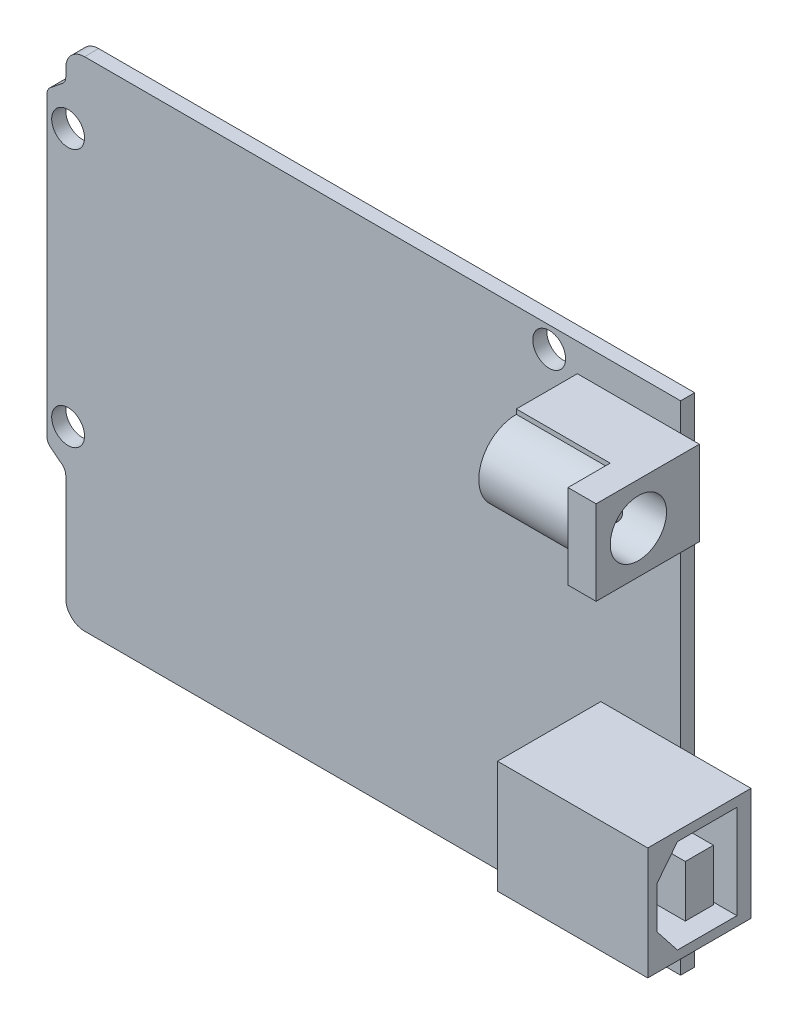
SolidWorks part; units mm, degrees
ref_plane "Front Plane" through (0, 0, 0) normal (0, 0, 1) x (1, 0, 0)
ref_plane "Top Plane" through (0, 0, 0) normal (0, 1, 0) x (1, 0, 0)
ref_plane "Right Plane" through (0, 0, 0) normal (1, 0, 0) x (0, 0, -1)
sketch "Sketch1" plane through (0, 0, 0) normal (0, 0, 1) x (1, 0, 0)
  line L0 (30, 26.5) -> (30, -26.5)
  line L1 (-37.5, 26.5) -> (37.5, 26.5)
  line L2 (-37.5, 26.5) -> (-37.5, -26.5)
  line L3 (-37.5, -26.5) -> (37.5, -26.5)
  line L4 (37.5, 26.5) -> (37.5, -26.5)
  line L5 (-37.5, 26.5) -> (37.5, -26.5) construction
  line L6 (-37.5, -26.5) -> (37.5, 26.5) construction
  circle A0 centre (-35.25, 19) radius 1.75
  circle A1 centre (-35.25, -8.5) radius 1.75
  circle A2 centre (16, 24.25) radius 1.75
  circle A3 centre (16, -24.25) radius 1.75
  point P0 (0, 0)
  dimension "D4" = 3.5
  dimension "D1" = 75
  dimension "D2" = 53
  dimension "D3" = 7.5
  dimension "D5" = 14
  dimension "D6" = 2.25
  dimension "D7" = 2.25
  dimension "D8" = 2.25
  dimension "D9" = 7.5
  dimension "D10" = 27.5
extrude "Boss-Extrude1" add sketch "Sketch1" along normal blind 1.5 contours L2 L3 L0 L1 A3 A2 A1 A0 | L4 L1 L0 L3
sketch "Sketch2" plane through (0, 0, 1.5) normal (0, 0, 1) x (1, 0, 0)
  line L0 (-37.5, -26.5) -> (37.5, -26.5) construction
  line L1 (-37.5, 26.5) -> (37.5, 26.5) construction
  line L2 (-37.5, 26.5) -> (-37.5, -26.5) construction
  line L3 (37.5, 26.5) -> (37.5, -26.5) construction
  line L4 (30, 26.5) -> (30, -26.5) construction
  line L5 (-37.5, -26.5) -> (37.5, -26.5)
  line L6 (-37.5, 26.5) -> (37.5, 26.5)
  line L7 (-37.5, 26.5) -> (-37.5, -26.5)
  line L8 (37.5, 26.5) -> (37.5, -26.5)
  line L9 (30, 26.5) -> (30, -26.5)
  line L10 (-37.5, 21.5442) -> (-35.5, 23.1319)
  line L11 (-35.5, 23.1319) -> (-35.5, 26.5)
  line L12 (-35.25, 19) -> (-35.25, -8.5) construction
  line L13 (-35.25, 5.25) -> (-14.1194, 5.25) construction
  line L14 (-35.5, -12.6319) -> (-35.5, -16)
  line L15 (-37.5, -11.0442) -> (-35.5, -12.6319)
  line L16 (-35.5, -16) -> (-35.5, -26.5)
  line M8 (-37.5, 26.5) -> (-37.5, -26.5)
  line M9 (-37.5, -26.5) -> (37.5, -26.5)
  line M11 (37.5, 26.5) -> (-37.5, 26.5)
  dimension "D1" = 2
extrude "Cut-Extrude1" cut sketch "Sketch2" against normal blind 2 contours L10 L11 M11 M8 | L16 L14 L15 M8 M9
fillet "Fillet1" radius 1 4 edges at (-35.5, 23.1319, 0.75) (-37.5, 21.5442, 0.75) (-35.5, -12.6319, 0.75) (-37.5, -11.0442, 0.75)
fillet "Fillet2" radius 2 2 edges at (-35.5, -26.5, 0.75) (-35.5, 26.5, 0.75)
sketch "Sketch3" plane through (0, 0, 1.5) normal (0, 0, 1) x (1, 0, 0)
  line L0 (-37.5, -26.5) -> (37.5, -26.5) construction
  line L1 (-37.5, 26.5) -> (37.5, 26.5) construction
  line L2 (37.5, 26.5) -> (37.5, -26.5) construction
  line L3 (-37.5, -26.5) -> (37.5, -26.5)
  line L4 (-37.5, 26.5) -> (37.5, 26.5)
  line L5 (37.5, 26.5) -> (37.5, -26.5)
  line L6 (30, 26.5) -> (30, 23.5)
  line L7 (30, 23.5) -> (32, 23.5)
  line L8 (32, 23.5) -> (32, 14.5)
  line L9 (32, 14.5) -> (30, 14.5)
  line L10 (30, 14.5) -> (30, -5.5)
  line L11 (30, -5.5) -> (37.5, -5.5)
  line L12 (37.5, -5.5) -> (37.5, -17.5)
  line L13 (37.5, -17.5) -> (30, -17.5)
  line L14 (30, -17.5) -> (30, -26.5)
  line L15 (30, 26.5) -> (30, -26.5) construction
  line M10 (37.5, -26.5) -> (37.5, 26.5)
  line M11 (37.5, 26.5) -> (-33.5, 26.5)
  dimension "D1" = 2
  dimension "D2" = 3
  dimension "D3" = 9
  dimension "D4" = 7.5
  dimension "D5" = 9
  dimension "D6" = 12
extrude "Cut-Extrude2" cut sketch "Sketch3" against normal blind 2 contours L10 L11 L5 L6 L7 L8 L9 M11 | L13 L14 L3 M10
sketch "Sketch4" plane through (0, 0, 1.5) normal (0, 0, 1) x (1, 0, 0)
  line L0 (37.5, -17.5) -> (30, -17.5) construction
  line L1 (37.5, -5.5) -> (37.5, -17.5) construction
  line L2 (30, -5.5) -> (37.5, -5.5) construction
  line L3 (37.5, -17.5) -> (30, -17.5)
  line L4 (37.5, -5.5) -> (37.5, -17.5)
  line L5 (30, -5.5) -> (37.5, -5.5)
  line L6 (30, -5.5) -> (21.5, -5.5)
  line L7 (21.5, -5.5) -> (21.5, -17.5)
  line L8 (21.5, -17.5) -> (30, -17.5)
  dimension "D1" = 16
extrude "Boss-Extrude2" add sketch "Sketch4" along normal blind 11
sketch "Sketch5" plane through (0, 0, 0) normal (0, 0, -1) x (-1, 0, 0)
  line L0 (-37.5, -17.5) -> (-30, -17.5) construction
  line L1 (-30, -5.5) -> (-37.5, -5.5) construction
  line L2 (-37.5, -5.5) -> (-37.5, -17.5) construction
  line L3 (-37.5, -17.5) -> (-30, -17.5)
  line L4 (-30, -5.5) -> (-37.5, -5.5)
  line L5 (-37.5, -5.5) -> (-37.5, -17.5)
  line L6 (-30, -5.5) -> (-30, -17.5)
  point P4 (0, 0)
extrude "Cut-Extrude3" cut sketch "Sketch5" against normal blind 1.5
sketch "Sketch6" plane through (37.5, 0, 0) normal (1, 0, 0) x (0, 0, -1)
  line L0 (-3, -16.5) -> (-3, -6.5)
  line L1 (-3, -6.5) -> (-9.3349, -6.5)
  line L2 (-9.3349, -6.5) -> (-11.5, -9.25)
  line L3 (-11.5, -9.25) -> (-11.5, -13.75)
  line L4 (-11.5, -13.75) -> (-9.3349, -16.5)
  line L5 (-9.3349, -16.5) -> (-3, -16.5)
  line L6 (-1.5, -5.5) -> (-1.5, -17.5) construction
  line L7 (-1.5, -5.5) -> (-12.5, -5.5) construction
  line L8 (-1.5, -17.5) -> (-12.5, -17.5) construction
  line L9 (-12.5, -17.5) -> (-12.5, -5.5) construction
  line L10 (-12.5, -5.5) -> (-1.5, -17.5) construction
  line L12 (-8.5, -8.75) -> (-5.5, -8.75)
  line L13 (-8.5, -8.75) -> (-8.5, -14.25)
  line L14 (-8.5, -14.25) -> (-5.5, -14.25)
  line L15 (-5.5, -8.75) -> (-5.5, -14.25)
  line L16 (-8.5, -8.75) -> (-5.5, -14.25) construction
  line L17 (-8.5, -14.25) -> (-5.5, -8.75) construction
  point P14 (-11.5, -11.5)
  point P15 (-3, -11.5)
  point P20 (-7, -11.5)
  dimension "D1" = 1.5
  dimension "D2" = 1
  dimension "D3" = 1
  dimension "D4" = 1
  dimension "D5" = 4.5
  dimension "D6" = 3.5
  dimension "D7" = 3
  dimension "D8" = 5.5
extrude "Cut-Extrude4" cut sketch "Sketch6" against normal offset from surface (12 mm away) 4 up to face at (21.5, -11.5, 7)
sketch "Sketch7" plane through (0, 0, 1.5) normal (0, 0, 1) x (1, 0, 0)
  line L0 (32, 14.5) -> (30, 14.5) construction
  line L1 (32, 23.5) -> (32, 14.5) construction
  line L2 (30, 23.5) -> (32, 23.5) construction
  line L3 (32, 14.5) -> (30, 14.5)
  line L4 (32, 23.5) -> (32, 14.5)
  line L5 (30, 23.5) -> (32, 23.5)
  line L6 (30, 23.5) -> (19, 23.5)
  line L7 (19, 23.5) -> (19, 14.5)
  line L8 (19, 14.5) -> (30, 14.5)
  dimension "D1" = 13
extrude "Boss-Extrude3" add sketch "Sketch7" along normal blind 11
sketch "Sketch8" plane through (0, 0, 0) normal (0, 0, -1) x (-1, 0, 0)
  line L0 (-30, 23.5) -> (-32, 23.5) construction
  line L1 (-32, 23.5) -> (-32, 14.5) construction
  line L2 (-32, 14.5) -> (-30, 14.5) construction
  line L3 (-30, 23.5) -> (-32, 23.5)
  line L4 (-32, 23.5) -> (-32, 14.5)
  line L5 (-32, 14.5) -> (-30, 14.5)
  line L6 (-30, 23.5) -> (-30, 14.5)
extrude "Cut-Extrude5" cut sketch "Sketch8" against normal blind 1.5
sketch "Sketch9" plane through (32, 0, 0) normal (1, 0, 0) x (0, 0, -1)
  line L0 (-3.5, 14.5) -> (-3.5, 23.5) construction
  line L1 (-1.5, 14.5) -> (-12.5, 14.5) construction
  line L2 (-1.5, 23.5) -> (-12.5, 23.5) construction
  line L3 (-12.5, 14.5) -> (-12.5, 23.5) construction
  line L4 (-12.5, 23.5) -> (-3.5, 14.5) construction
  circle A0 centre (-8, 19) radius 3
  circle A1 centre (-8, 19) radius 0.75
  dimension "D2" = 6
  dimension "D3" = 1.5
  dimension "D1" = 9
extrude "Cut-Extrude6" cut sketch "Sketch9" against normal offset from surface (9 mm away) 4 up to face at (19, 19, 7)
sketch "Sketch10" plane through (32, 0, 0) normal (1, 0, 0) x (0, 0, -1)
  circle A1 centre (-8, 19) radius 0.75
  circle A2 centre (-8, 19) radius 0.75
  dimension "D1" = 0
extrude "Cut-Extrude7" cut sketch "Sketch10" against normal blind 2
fillet "Fillet3" radius 0.75 1 edges at (30, 19, 7.25)
sketch "Sketch11" plane through (19, 0, 0) normal (-1, 0, 0) x (0, 0, 1)
  line L0 (12.5, 14.5) -> (1.5, 14.5) construction
  line L1 (12.5, 23.5) -> (12.5, 14.5) construction
  line L2 (12.5, 23.5) -> (1.5, 23.5) construction
  line L3 (12.5, 14.5) -> (8, 14.5)
  line L4 (12.5, 23.5) -> (12.5, 14.5)
  line L5 (12.5, 23.5) -> (8, 23.5)
  line L6 (8, 15) -> (8, 14.5)
  line L7 (8, 14.5) -> (8, 15)
  line L8 (8, 23) -> (8, 23.5)
  circle A0 centre (8, 19) radius 3 construction
  arc A1 (8, 16) -> (8, 22) centre (8, 19) ccw construction
  arc A2 (8, 15) -> (8, 23) centre (8, 19) ccw
  circle A3 centre (8, 19) radius 4 construction
  circle A4 centre (8, 19) radius 3 construction
  line M3 (1.5, 14.5) -> (12.5, 14.5)
  line M4 (12.5, 14.5) -> (12.5, 23.5)
  line M5 (12.5, 23.5) -> (1.5, 23.5)
  dimension "D1" = 1
extrude "Cut-Extrude8" cut sketch "Sketch11" against normal offset from surface (10 mm away) 3 contours A2 L6 L8 M3 M4 M5 up to face at (32, 19, 5)
